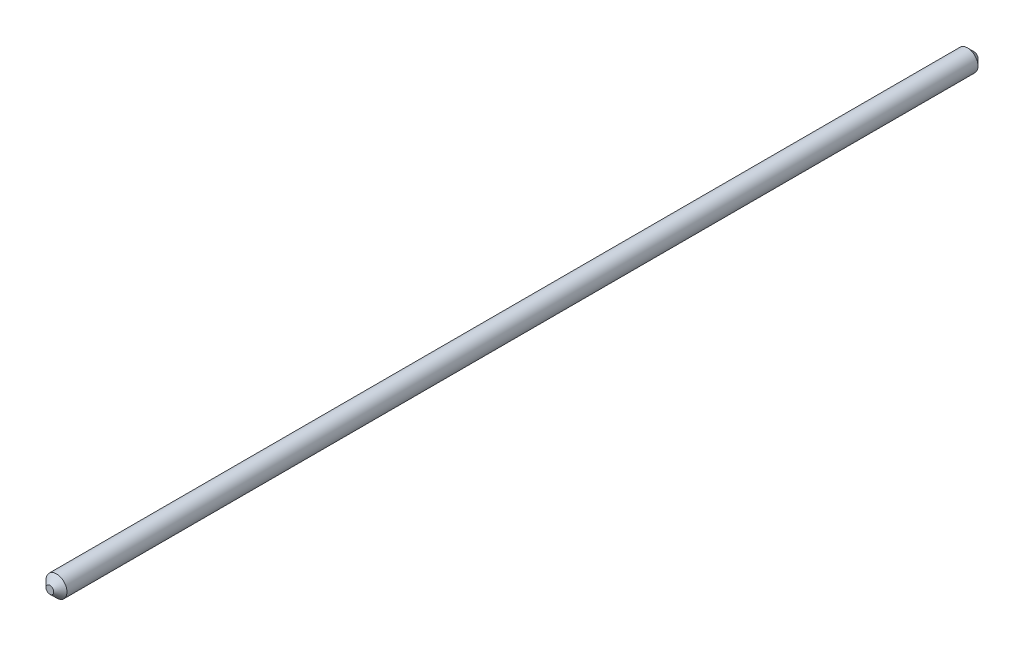
SolidWorks part; units mm, degrees
material "Cast Stainless Steel"
ref_plane "Front Plane" through (0, 0, 0) normal (0, 0, 1) x (1, 0, 0)
ref_plane "Top Plane" through (0, 0, 0) normal (0, 1, 0) x (1, 0, 0)
ref_plane "Right Plane" through (0, 0, 0) normal (1, 0, 0) x (0, 0, -1)
sketch "Sketch1" plane through (0, 0, 0) normal (0, 0, 1) x (1, 0, 0)
  circle A0 centre (0, 0) radius 3.175
  dimension "D1" = 6.35
extrude "Boss-Extrude1" add sketch "Sketch1" along normal blind 280
chamfer "Chamfer1" distance 2 angle 45 2 edges at (3.175, 0, 280) (3.175, 0, 0)
